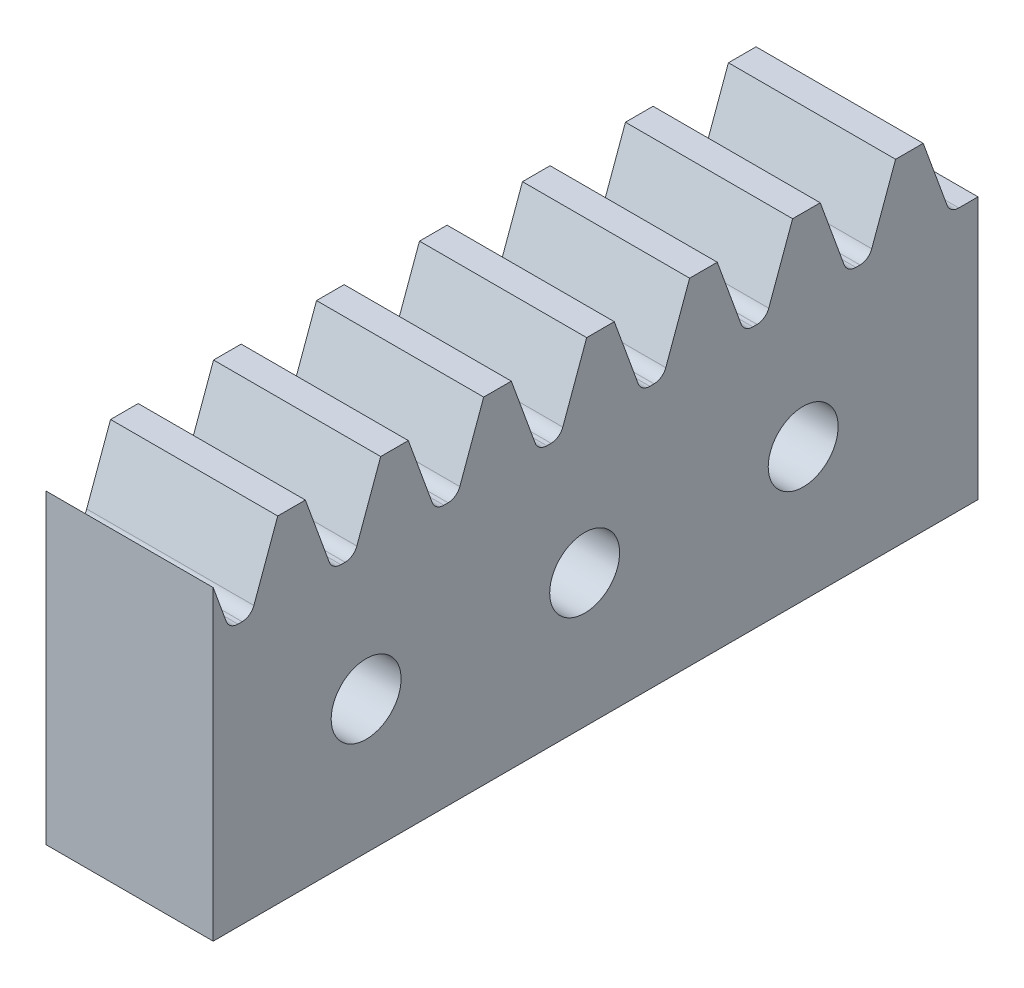
SolidWorks part; units mm, degrees
ref_plane "Front Plane" through (0, 0, 0) normal (0, 0, 1) x (1, 0, 0)
ref_plane "Top Plane" through (0, 0, 0) normal (0, 1, 0) x (1, 0, 0)
ref_plane "Right Plane" through (0, 0, 0) normal (1, 0, 0) x (0, 0, -1)
sketch "Esquisse1" plane through (0, 0, 0) normal (0, 0, 1) x (1, 0, 0)
  line L1 (-12, 15) -> (12, 15)
  line L2 (-12, 15) -> (-12, -15)
  line L3 (-12, -15) -> (12, -15)
  line L4 (12, 15) -> (12, -15)
  point P4 (0, -15)
  point P5 (-12, 0)
  dimension "D1" = 24
  dimension "D2" = 30
extrude "Main Extrusion" add sketch "Esquisse1" along normal blind 30
sketch "Esquisse3" plane through (0, 0, 0) normal (0, 0, -1) x (-1, 0, 0)
  line L0 (-5.2, -1.6) -> (-5.2, -5.4)
  line L1 (-5.2, -5.4) -> (-4.2, -5.4)
  line L2 (-4.2, -5.4) -> (-4.2, -8.2)
  line L3 (-4.2, -8.2) -> (-5.2, -8.2)
  line L4 (-5.2, -8.2) -> (-5.2, -12)
  line L5 (-5.2, -12) -> (-1.4, -12)
  line L6 (-1.4, -12) -> (-1.4, -11)
  line L7 (-1.4, -11) -> (1.4, -11)
  line L8 (1.4, -11) -> (1.4, -12)
  line L9 (1.4, -12) -> (5.2, -12)
  line L10 (5.2, -12) -> (5.2, -8.2)
  line L11 (5.2, -8.2) -> (4.2, -8.2)
  line L12 (4.2, -8.2) -> (4.2, -5.4)
  line L13 (4.2, -5.4) -> (5.2, -5.4)
  line L14 (5.2, -5.4) -> (5.2, -1.6)
  line L15 (5.2, -1.6) -> (1.4, -1.6)
  line L16 (1.4, -1.6) -> (1.4, -2.6)
  line L17 (1.4, -2.6) -> (-1.4, -2.6)
  line L18 (-1.4, -2.6) -> (-1.4, -1.6)
  line L19 (-1.4, -1.6) -> (-5.2, -1.6)
  line L21 (12, -15) -> (-12, -15) construction
  point P20 (0, -11)
  point P24 (0, -15)
  dimension "D1" = 2.8
  dimension "D2" = 10.4
  dimension "D3" = 1
  dimension "D4" = 1
  dimension "D5" = 3
extrude "Main Riding Hole" cut sketch "Esquisse3" against normal through all
sketch "Esquisse4" plane through (-12, 0, 0) normal (-1, 0, 0) x (0, 0, 1)
  line L1 (0, -8.2) -> (0, -5.4) construction
  line L2 (0, 15) -> (0, -15) construction
  circle A0 centre (5, -6.8) radius 2.25
  point P5 (0, -6.8)
  dimension "D1" = 4.5
  dimension "D2" = 5
extrude "TractorHole" cut sketch "Esquisse4" against normal blind 8
mirror "TractorHoleSymetry" about plane through (0, 0, 0) normal (1, 0, 0) of "TractorHole"
sketch "Esquisse5" plane through (0, 0, 0) normal (1, 0, 0) x (0, 0, -1)
  line L0 (-45, 5) -> (-45, 35)
  line L2 (-45, 35) -> (-25, 35)
  line L3 (-25, 35) -> (-21.4735, 15)
  line L4 (-45, 5) -> (0, 5)
  line L5 (-21.4735, 15) -> (35, 15)
  line L6 (-30, -15) -> (-30, 15) construction
  line L7 (35, 15) -> (35, 3)
  line L8 (-30, -15) -> (0, -15) construction
  line L9 (0, 5) -> (0, 3)
  line L10 (0, -15) -> (0, 15) construction
  line L11 (0, 3) -> (35, 3)
  line L12 (-30, -15) -> (0, -15) construction
  dimension "D1" = 30
  dimension "D2" = 20
  dimension "D3" = 18
  dimension "D4" = 15
  dimension "D5" = 12
  dimension "D6" = 100
  dimension "D7" = 35
  dimension "D8" = 20
extrude "ImpactPiece" add sketch "Esquisse5" against normal mid plane 9
fillet "Congé1" radius 3 2 edges at (-4.5, 15, 25.7367) (4.5, 15, 25.7367)
sketch "Esquisse8" plane through (0, 0, 0) normal (1, 0, 0) x (0, 0, -1)
  line L0 (30, 15) -> (31.2284, 18.375)
  line L1 (31.2284, 18.375) -> (32.4927, 18.375)
  line L2 (32.4927, 18.375) -> (33.7211, 15)
  line L3 (30, 15) -> (29.0087, 15) construction
  line L4 (30, 15) -> (33.7211, 15)
  line L5 (30.1365, 15.375) -> (28.8722, 15.375) construction
  line L6 (30, 15) -> (30, 1.1813) construction
  line L7 (29.0087, 15) -> (28.3262, 16.875) construction
  line L8 (28.3262, 16.875) -> (33.0386, 16.875) construction
  line L9 (35, 15) -> (0, 15) construction
  line L10 (35, 3) -> (35, 15) construction
  dimension "D1" = 20
  dimension "D2" = 1.5
  dimension "D3" = 3.375
  dimension "D4" = 4.7124
  dimension "D5" = 3
  dimension "D6" = 5
extrude "Teeth" add sketch "Esquisse8" along normal mid plane 9
fillet "Congé3" radius 0.57 2 edges at (0, 15, -30) (0, 15, -33.7211)
pattern_linear "TeethRepetition" count 8 spacing 4.7124 along (0, 0, 1) of "Teeth", "Congé3"
sketch "Esquisse9" plane through (4.5, 0, 0) normal (1, 0, 0) x (0, 0, -1)
  line L0 (0, -15) -> (0, 15) construction
  line L1 (-20, 18.375) -> (35, 18.375)
  line L2 (-20, 18.375) -> (-20, 3)
  line L3 (-20, 3) -> (35, 3)
  line L4 (35, 18.375) -> (35, 3)
  line L5 (35, 3) -> (35, 15) construction
  line L8 (32.4927, 18.375) -> (31.2284, 18.375) construction
  dimension "D3" = 20
extrude "Bracket" cut sketch "Esquisse9" along normal mid plane 1.35
sketch "Esquisse10" plane through (4.5, 0, 0) normal (-1, 0, 0) x (0, 0, 1)
  line L4 (0, 3) -> (-35, 3) construction
  line L5 (-35, 3) -> (-35, 15) construction
  circle A0 centre (-27, 9.1) radius 1.6
  dimension "D1" = 3.2
  dimension "D2" = 6.1
  dimension "D3" = 8
extrude "BracketHole" cut sketch "Esquisse10" against normal through all both and the other way through all
pattern_linear "BracketHoleRepetition" count 5 spacing 10 along (0, 0, 1) of "BracketHole"
mirror "Symétrie1" about plane through (0, 0, 0) normal (1, 0, 0) of "Bracket"
sketch "Esquisse11" plane through (0, 0, 0) normal (0, 0, -1) x (-1, 0, 0)
  line L0 (12, 15) -> (12, -15) construction
  line L1 (12, 0.4) -> (4.5, 0.4)
  line L2 (12, 0.4) -> (12, 5.9)
  line L3 (12, 5.9) -> (4.5, 5.9)
  line L4 (4.5, 0.4) -> (4.5, 5.9)
  line L5 (4.5, 18) -> (4.5, 3) construction
  line L6 (5.2, -1.6) -> (1.4, -1.6) construction
  line L7 (4.5, 35) -> (4.5, 5) construction
  line L8 (4.5, 20) -> (12, 20)
  line L9 (4.5, 20) -> (4.5, 12.4)
  line L10 (4.5, 12.4) -> (12, 12.4)
  line L11 (12, 20) -> (12, 12.4)
  line L12 (12, 15) -> (12, -15) construction
  dimension "D1" = 2
  dimension "D2" = 5.5
  dimension "D3" = 6.5
extrude "RailHole" cut sketch "Esquisse11" against normal blind 20
sketch "Esquisse12" plane through (4.5, 0, 0) normal (1, 0, 0) x (0, 0, -1)
  line L0 (-45, 30) -> (-40, 35)
  line L1 (-45, 35) -> (-45, 5) construction
  line L2 (-25, 35) -> (-45, 35) construction
  line L3 (-40, 35) -> (-45, 35)
  line L4 (-45, 35) -> (-45, 30)
  dimension "D1" = 5
extrude "TopImpactCut" cut sketch "Esquisse12" against normal through all
mirror "Symétrie2" about plane through (12, 15, 30) normal (-1, 0, 0) of bodies 117
sketch "Esquisse13" plane through (0, 0, -35) normal (0, 0, -1) x (-1, 0, 0)
  line L0 (4.5, 35) -> (-4.5, 35) construction
  line L1 (-12, -15) -> (12, -15)
  line L2 (-12, -15) -> (-12, 35)
  line L3 (-12, 35) -> (12, 35)
  line L4 (12, -15) -> (12, 35)
extrude "MakerBeamMainHole" cut sketch "Esquisse13" against normal through all
sketch "Sketch1" plane through (0, 35, 0) normal (0, 1, 0) x (1, 0, 0)
  line L0 (12, 0) -> (12, -45)
  line L1 (12, -45) -> (36, -45)
  line L2 (36, -45) -> (36, 0)
  line L8 (28.5, -45) -> (19.5, -45) construction
  line L9 (36, 0) -> (12, 0)
extrude "KeepOnlyTractor1" cut sketch "Sketch1" against normal through all
